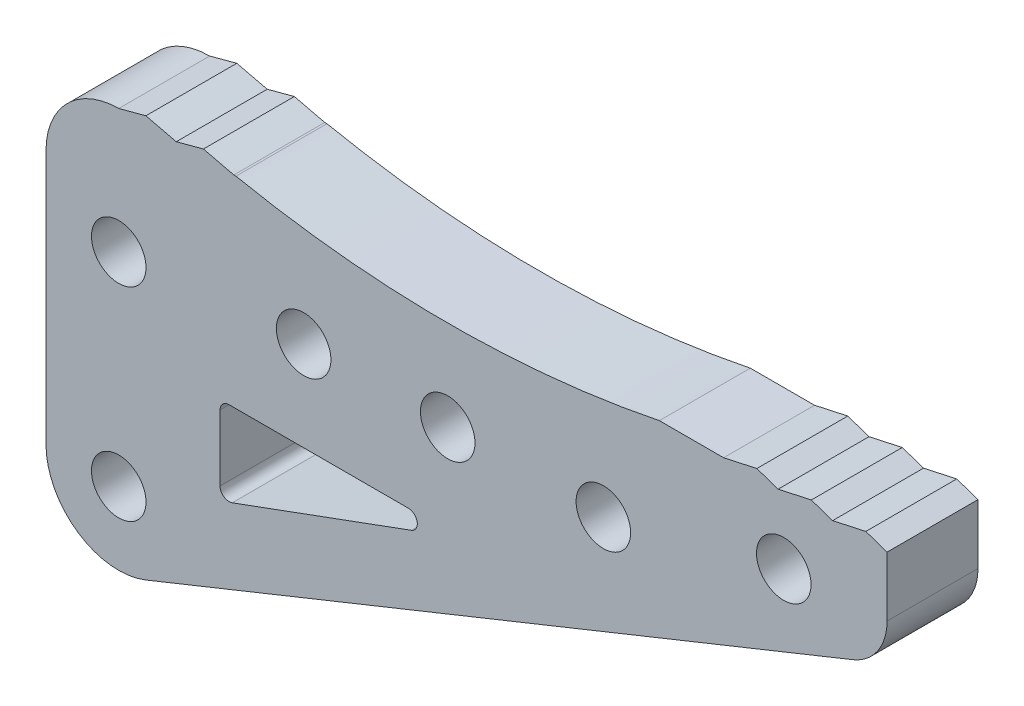
SolidWorks part; units mm, degrees
ref_plane "Front Plane" through (0, 0, 0) normal (0, 0, 1) x (1, 0, 0)
ref_plane "Top Plane" through (0, 0, 0) normal (0, 1, 0) x (1, 0, 0)
ref_plane "Right Plane" through (0, 0, 0) normal (1, 0, 0) x (0, 0, -1)
sketch "Sketch1" plane through (0, 0, 0) normal (0, 0, 1) x (1, 0, 0)
  line L0 (1.081, -0.1469) -> (131.081, -0.1469) construction
  line L1 (0, 0) -> (130, 0)
  line L2 (84.5973, 21.2918) -> (84.5973, 35.2918)
  line L3 (88.5973, 39.2918) -> (130.852, 39.2918)
  line L4 (130.852, 39.2918) -> (130.852, 36.0095)
  line L5 (128.9719, 33.2263) -> (90.0905, 17.581)
  line L6 (88.5973, 39.2918) -> (88.5973, 39.6918)
  line L7 (88.5973, 39.6918) -> (130.852, 39.6918)
  line L8 (130.852, 39.6918) -> (130.852, 39.2918)
  line L9 (130.852, 39.2918) -> (129.6834, 39.6918)
  line L10 (129.6834, 39.6918) -> (127.8554, 39.2918)
  line L11 (127.8554, 39.2918) -> (126.6869, 39.6918)
  line L12 (126.6869, 39.6918) -> (124.8589, 39.2918)
  line L13 (124.8589, 39.2918) -> (123.6903, 39.6918)
  line L14 (123.6903, 39.6918) -> (121.8624, 39.2918)
  line L15 (88.5973, 39.2918) -> (90.0905, 39.6918)
  line L16 (90.0905, 39.6918) -> (91.7618, 39.2918)
  line L17 (91.7618, 39.2918) -> (93.2549, 39.6918)
  line L18 (93.2549, 39.6918) -> (94.9262, 39.2918)
  line L19 (94.1671, 27.7191) -> (94.1671, 24.1019)
  line L20 (94.8395, 23.6325) -> (104.6908, 27.2498)
  line L21 (104.5184, 28.2191) -> (94.6671, 28.2191)
  circle A0 centre (88.5973, 21.2918) radius 4
  circle A1 centre (88.5973, 32.4608) radius 4
  arc A2 (95.0468, 39.2918) -> (118.3305, 39.2918) centre (106.6887, 96.4533) ccw
  arc A3 (88.5973, 39.2918) -> (84.5973, 35.2918) centre (88.5973, 35.2918) ccw
  circle A4 centre (98.7665, 33.1569) radius 1.5
  circle A5 centre (106.6887, 33.1569) radius 1.5
  circle A6 centre (115.2485, 33.1569) radius 1.5
  circle A7 centre (125.1691, 35.6496) radius 1.5
  arc A8 (94.1671, 27.7191) -> (94.6671, 28.2191) centre (94.6671, 27.7191) cw
  arc A9 (94.8395, 23.6325) -> (94.1671, 24.1019) centre (94.6671, 24.1019) cw
  arc A10 (104.6908, 27.2498) -> (104.5184, 28.2191) centre (104.5184, 27.7191) ccw
  circle A11 centre (88.5973, 32.4608) radius 1.5
  circle A12 centre (88.5973, 21.2918) radius 1.5
  arc A13 (128.9719, 33.2263) -> (130.852, 36.0095) centre (127.852, 36.0095) ccw
  point P19 (84.5973, 39.2918)
  dimension "D3" = 8
  dimension "D4" = 8
  dimension "D6" = 4
  dimension "D8" = 3
  dimension "D9" = 3
  dimension "D10" = 3
  dimension "D11" = 3
  dimension "D12" = 0.5
  dimension "D13" = 0.5
  dimension "D14" = 0.5
  dimension "D15" = 3
  dimension "D16" = 3
  dimension "D17" = 3
  dimension "D1" = 130
  dimension "D2" = 130
  dimension "D5" = 18
  dimension "D7" = 0.4
extrude "Boss-Extrude1" add sketch "Sketch1" along normal blind 5 contours A1 A11 | A0 A12 | L16 L15 L3 | L18 L17 L3 | L13 L14 L3 | L11 L12 L3 | L9 L10 L3 | L3 A3 L2 A1 A0 L5 L4 A2 A10 L20 A9 L19 A8 L21 A7 A6 A5 A4
